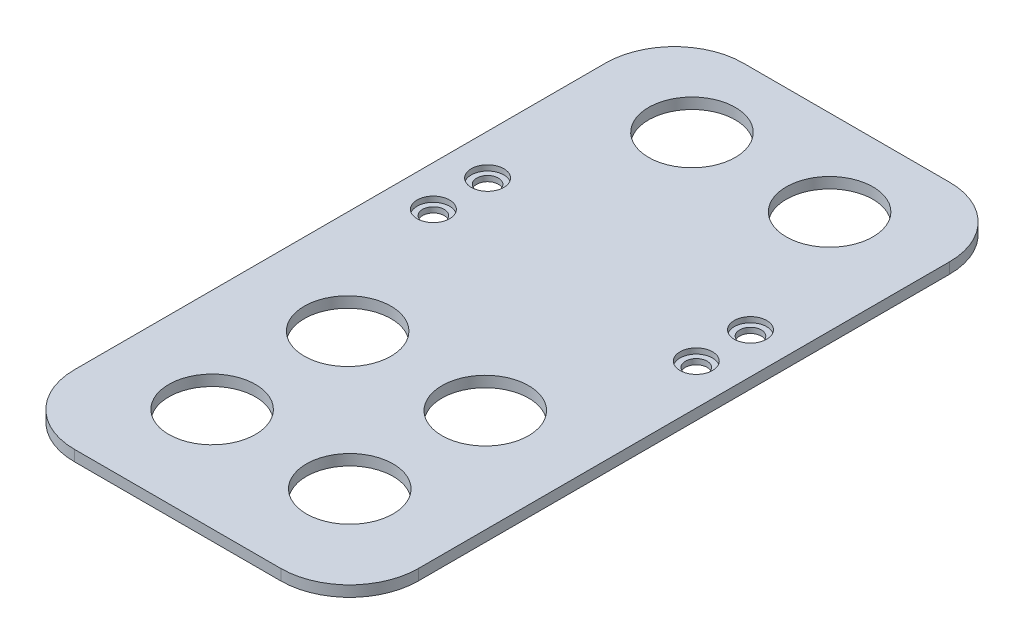
SolidWorks part; units mm, degrees
material "5052-H32"
ref_plane "Front Plane" through (0, 0, 0) normal (0, 0, 1) x (1, 0, 0)
ref_plane "Top Plane" through (0, 0, 0) normal (0, 1, 0) x (1, 0, 0)
ref_plane "Right Plane" through (0, 0, 0) normal (1, 0, 0) x (0, 0, -1)
sketch "Sketch1" plane through (0, 0, 0) normal (0, 1, 0) x (1, 0, 0)
  line L1 (19.05, -61.72) -> (-19.05, -61.72)
  line L2 (31.75, -49.02) -> (31.75, 49.02)
  line L3 (19.05, 61.72) -> (-19.05, 61.72)
  line L4 (-31.75, -49.02) -> (-31.75, 49.02)
  line L5 (31.75, -61.72) -> (-31.75, 61.72) construction
  line L6 (31.75, 61.72) -> (-31.75, -61.72) construction
  arc A0 (-19.05, 61.72) -> (-31.75, 49.02) centre (-19.05, 49.02) ccw
  arc A1 (31.75, 49.02) -> (19.05, 61.72) centre (19.05, 49.02) ccw
  arc A2 (31.75, -49.02) -> (19.05, -61.72) centre (19.05, -49.02) cw
  arc A3 (-19.05, -61.72) -> (-31.75, -49.02) centre (-19.05, -49.02) cw
  circle A4 centre (-12.7, 45.91) radius 8
  circle A5 centre (12.7, 45.91) radius 8
  circle A6 centre (-12.7, -42.64) radius 8
  circle A7 centre (12.7, -42.64) radius 8
  circle A8 centre (12.7, -17.63) radius 8
  circle A9 centre (-12.7, -17.63) radius 8
  circle A10 centre (-24.26, 19.75) radius 2
  circle A11 centre (-24.26, 9.75) radius 2
  circle A12 centre (24.26, 19.75) radius 2
  circle A13 centre (24.26, 9.75) radius 2
  point P0 (0, 0)
  dimension "D3" = 12.7
  dimension "D4" = 12.7
  dimension "D5" = 12.7
  dimension "D6" = 12.7
  dimension "D7" = 16
  dimension "D8" = 16
  dimension "D13" = 16
  dimension "D14" = 16
  dimension "D15" = 16
  dimension "D16" = 16
  dimension "D23" = 4
  dimension "D24" = 4
  dimension "D27" = 4
  dimension "D28" = 4
  dimension "D1" = 123.44
  dimension "D2" = 63.5
  dimension "D9" = 25.4
  dimension "D10" = 12.7
  dimension "D11" = 15.81
  dimension "D12" = 15.81
  dimension "D17" = 19.08
  dimension "D18" = 19.08
  dimension "D19" = 25.01
  dimension "D20" = 25.01
  dimension "D21" = 25.4
  dimension "D22" = 25.4
  dimension "D25" = 10
  dimension "D26" = 10
  dimension "D29" = 48.52
  dimension "D30" = 24.26
  dimension "D31" = 51.97
  dimension "D32" = 51.97
extrude "Boss-Extrude1" add sketch "Sketch1" along normal blind 2
sketch "Sketch2" plane through (0, 2, 0) normal (0, 1, 0) x (1, 0, 0)
  circle A0 centre (-24.26, 19.75) radius 3
  circle A1 centre (-24.26, 9.75) radius 3
  circle A2 centre (24.26, 19.75) radius 3
  circle A3 centre (24.26, 9.75) radius 3
  dimension "D1" = 6
  dimension "D2" = 6
  dimension "D3" = 6
  dimension "D4" = 6
extrude "Cut-Extrude1" cut sketch "Sketch2" against normal blind 1
